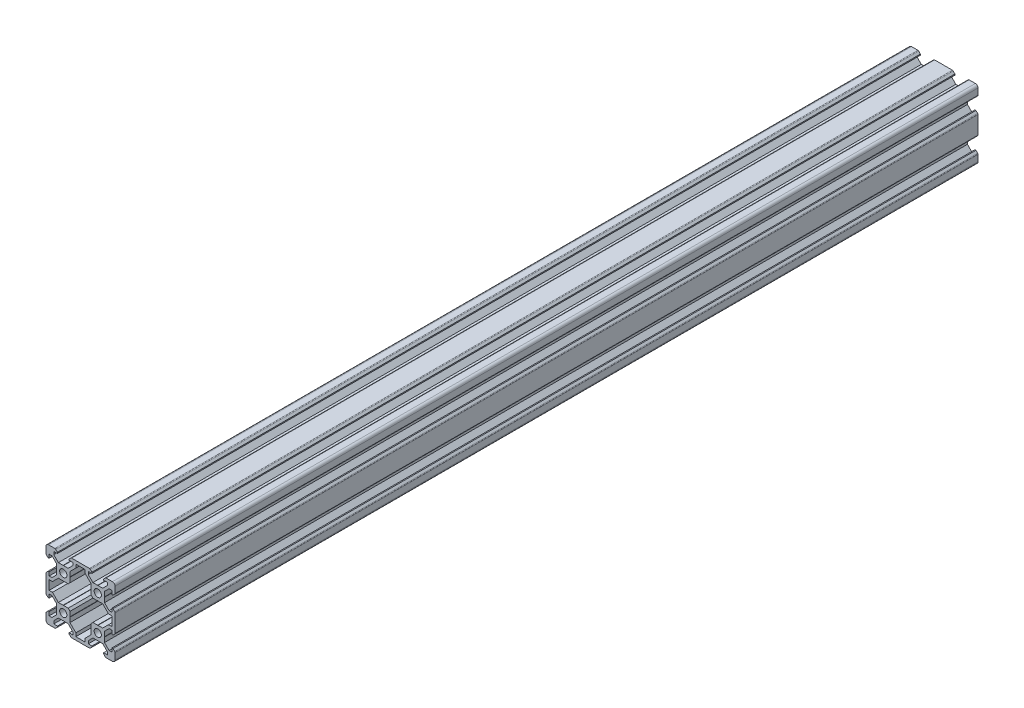
SolidWorks part; units mm, degrees
material "6063-T5"
ref_plane "Front" through (0, 0, 0) normal (0, 0, 1) x (1, 0, 0)
ref_plane "Top" through (0, 0, 0) normal (0, 1, 0) x (1, 0, 0)
ref_plane "Right" through (0, 0, 0) normal (1, 0, 0) x (0, 0, -1)
sketch "Sketch1" plane through (0, 0, 0) normal (0, 0, 1) x (1, 0, 0)
  line L0 (-8.5, 10) -> (-10, 8.5) construction
  line L1 (-8.5, 10) -> (-4.8628, 10)
  line L2 (-10, 8.5) -> (-10, 4.8628)
  line L3 (10, 24.069) -> (10, -33.8154) construction
  line L4 (4.8628, 10) -> (15.1372, 10)
  line L5 (-10, 10) -> (10, -10) construction
  line L6 (-10, -10) -> (10, 10) construction
  line L7 (4.8628, -30) -> (15.1372, -30)
  line L8 (-8.2, -5.5) -> (-8.2, -3.3865)
  line L9 (-5.5, 8.2) -> (-3.3865, 8.2)
  line L10 (-8.2, -12.7) -> (-8.2, -7.3)
  line L11 (-3.9005, 2.8395) -> (-6.561, 5.5)
  line L12 (-6.561, 5.5) -> (-8.2, 5.5)
  line L13 (-2.8395, -3.9005) -> (-0.1, -3.9005)
  line L14 (-3.9005, -2.8395) -> (-3.9005, -0.1)
  line L15 (-2.8395, 3.9005) -> (-0.1, 3.9005)
  line L16 (3.9005, -2.8395) -> (3.9005, -0.1)
  line L17 (-8.2, 3.3865) -> (-8.81, 3.3865)
  line L18 (-8.81, 3.3865) -> (-9.7976, 4.3741)
  line L19 (17.1605, -23.9005) -> (14.5, -26.561)
  line L20 (-2.8395, 3.9005) -> (-5.5, 6.561)
  line L21 (-5.5, 6.561) -> (-5.5, 8.2)
  line L22 (-3.3865, 8.2) -> (-3.3865, 8.81)
  line L23 (-3.3865, 8.81) -> (-4.3741, 9.7976)
  line L24 (0, 24.069) -> (0, -33.8154) construction
  line L25 (3.3865, 8.81) -> (4.3741, 9.7976)
  line L26 (3.3865, 8.2) -> (3.3865, 8.81)
  line L27 (5.5, 6.561) -> (5.5, 8.2)
  line L28 (2.8395, 3.9005) -> (5.5, 6.561)
  line L29 (3.3865, 8.2) -> (5.5, 8.2)
  line L30 (16.0995, -22.8395) -> (13.439, -25.5)
  line L31 (-0.1, 3.9005) -> (0, 3.8005)
  line L32 (0.1, 3.9005) -> (0, 3.8005)
  line L33 (0.1, 3.9005) -> (2.8395, 3.9005)
  line L34 (25.9287, 0) -> (-28.3459, 0) construction
  line L35 (-0.1, -3.9005) -> (0, -3.8005)
  line L36 (0.1, -3.9005) -> (0, -3.8005)
  line L37 (0.1, -3.9005) -> (2.8395, -3.9005)
  line L38 (-3.9005, 0.1) -> (-3.8005, 0)
  line L39 (-3.8005, 0) -> (-3.9005, -0.1)
  line L40 (-3.9005, 0.1) -> (-3.9005, 2.8395)
  line L41 (3.9005, 0.1) -> (3.8005, 0)
  line L42 (3.8005, 0) -> (3.9005, -0.1)
  line L43 (3.9005, 0.1) -> (3.9005, 2.8395)
  line L44 (14.5, -26.561) -> (14.5, -28.2)
  line L45 (16.6135, -28.2) -> (14.5, -28.2)
  line L46 (16.6135, -28.2) -> (16.6135, -28.81)
  line L47 (3.9005, 2.8395) -> (6.561, 5.5)
  line L48 (16.6135, -28.81) -> (15.6259, -29.7976)
  line L49 (7.3, -28.2) -> (10, -28.2)
  line L50 (-2.8395, -3.9005) -> (-5.5, -6.561)
  line L51 (-3.9005, -2.8395) -> (-6.561, -5.5)
  line L52 (10, -28.2) -> (12.7, -28.2)
  line L53 (-6.561, -5.5) -> (-8.2, -5.5)
  line L54 (-8.81, -3.3865) -> (-9.7976, -4.3741)
  line L55 (-8.2, -3.3865) -> (-8.81, -3.3865)
  line L56 (7.3, -28.2) -> (7.3, -26.239)
  line L57 (7.3, -26.239) -> (6.561, -25.5)
  line L58 (12.7, -28.2) -> (12.7, -26.239)
  line L59 (12.7, -26.239) -> (13.439, -25.5)
  line L60 (-8.2, 3.3865) -> (-8.2, 5.5)
  line L61 (-10, -4.8628) -> (-10, -15.1372)
  line L62 (-28.3459, -10) -> (-10, -10) construction
  line L63 (-3.9005, -20.1) -> (-3.9005, -22.8395)
  line L64 (-3.9005, -20.1) -> (-3.8005, -20)
  line L65 (-3.8005, -20) -> (-3.9005, -19.9)
  line L66 (3.9005, -20.1) -> (3.9005, -22.8395)
  line L67 (3.9005, -20.1) -> (3.8005, -20)
  line L68 (3.8005, -20) -> (3.9005, -19.9)
  line L69 (12.7, 8.2) -> (12.7, 6.239)
  line L70 (7.3, 8.2) -> (7.3, 6.239)
  line L71 (3.9005, -17.1605) -> (3.9005, -19.9)
  line L72 (-3.9005, -17.1605) -> (-3.9005, -19.9)
  line L73 (-3.9005, -17.1605) -> (-6.561, -14.5)
  line L74 (-6.561, -14.5) -> (-8.2, -14.5)
  line L75 (-8.2, -16.6135) -> (-8.81, -16.6135)
  line L76 (-8.81, -16.6135) -> (-9.7976, -15.6259)
  line L77 (10, 8.2) -> (12.7, 8.2)
  line L78 (7.3, 8.2) -> (10, 8.2)
  line L79 (-2.8395, -16.0995) -> (-5.5, -13.439)
  line L80 (-2.8395, -16.0995) -> (-0.1, -16.0995)
  line L81 (-0.1, -16.0995) -> (0, -16.1995)
  line L82 (0.1, -16.0995) -> (0, -16.1995)
  line L83 (0.1, -16.0995) -> (2.8395, -16.0995)
  line L84 (7.3, 6.239) -> (6.561, 5.5)
  line L85 (-8.2, -16.6135) -> (-8.2, -14.5)
  line L86 (14.5, 6.561) -> (14.5, 8.2)
  line L87 (2.8395, -23.9005) -> (5.5, -26.561)
  line L88 (-2.8395, -23.9005) -> (-5.5, -26.561)
  line L89 (-0.1, -23.9005) -> (0, -23.8005)
  line L90 (0.1, -23.9005) -> (0, -23.8005)
  line L91 (0.1, -23.9005) -> (2.8395, -23.9005)
  line L92 (-2.8395, -23.9005) -> (-0.1, -23.9005)
  line L93 (-10, -28.5) -> (-10, -24.8628)
  line L94 (16.6135, 8.2) -> (14.5, 8.2)
  line L95 (16.6135, 8.81) -> (15.6259, 9.7976)
  line L96 (-8.81, -23.3865) -> (-9.7976, -24.3741)
  line L97 (-8.2, -23.3865) -> (-8.81, -23.3865)
  line L98 (16.6135, 8.2) -> (16.6135, 8.81)
  line L99 (16.0995, 2.8395) -> (13.439, 5.5)
  line L100 (-8.2, -23.3865) -> (-8.2, -25.5)
  line L101 (-6.561, -25.5) -> (-8.2, -25.5)
  line L102 (12.7, 6.239) -> (13.439, 5.5)
  line L103 (3.9005, -22.8395) -> (6.561, -25.5)
  line L104 (-3.9005, -22.8395) -> (-6.561, -25.5)
  line L105 (-5.5, -28.2) -> (-3.3865, -28.2)
  line L106 (3.3865, -28.2) -> (5.5, -28.2)
  line L107 (3.3865, -28.2) -> (3.3865, -28.81)
  line L108 (3.3865, -28.81) -> (4.3741, -29.7976)
  line L109 (-3.3865, -28.2) -> (-3.3865, -28.81)
  line L110 (-3.3865, -28.81) -> (-4.3741, -29.7976)
  line L111 (-8.5, -30) -> (-4.8628, -30)
  line L112 (17.1605, 3.9005) -> (14.5, 6.561)
  line L113 (-5.5, -26.561) -> (-5.5, -28.2)
  line L114 (5.5, -26.561) -> (5.5, -28.2)
  line L115 (-6.239, -7.3) -> (-8.2, -7.3)
  line L116 (-5.5, -6.561) -> (-6.239, -7.3)
  line L117 (3.9005, -2.8395) -> (2.8395, -3.9005)
  line L118 (2.8395, -16.0995) -> (3.9005, -17.1605)
  line L119 (-6.239, -12.7) -> (-8.2, -12.7)
  line L120 (-5.5, -13.439) -> (-6.239, -12.7)
  line L121 (16.0995, -2.8395) -> (17.1605, -3.9005)
  line L122 (17.1605, -16.0995) -> (16.0995, -17.1605)
  line L123 (28.2, -16.6135) -> (28.81, -16.6135)
  line L124 (20.1, -3.9005) -> (20, -3.8005)
  line L125 (10, -10) -> (25.9287, -10) construction
  line L126 (19.9, -3.9005) -> (20, -3.8005)
  line L127 (19.9, -3.9005) -> (17.1605, -3.9005)
  line L128 (22.8395, -3.9005) -> (20.1, -3.9005)
  line L129 (23.9005, -2.8395) -> (23.9005, -0.1)
  line L130 (23.8005, 0) -> (23.9005, -0.1)
  line L131 (23.9005, 0.1) -> (23.8005, 0)
  line L132 (23.9005, 0.1) -> (23.9005, 2.8395)
  line L133 (20.1, 3.9005) -> (20, 3.8005)
  line L134 (19.9, 3.9005) -> (20, 3.8005)
  line L135 (16.0995, 0.1) -> (16.1995, 0)
  line L136 (16.1995, 0) -> (16.0995, -0.1)
  line L137 (22.8395, 3.9005) -> (20.1, 3.9005)
  line L138 (19.9, 3.9005) -> (17.1605, 3.9005)
  line L139 (16.0995, 0.1) -> (16.0995, 2.8395)
  line L140 (16.0995, -2.8395) -> (16.0995, -0.1)
  line L141 (20.1, -23.9005) -> (20, -23.8005)
  line L142 (19.9, -23.9005) -> (20, -23.8005)
  line L143 (19.9, -23.9005) -> (17.1605, -23.9005)
  line L144 (22.8395, -23.9005) -> (20.1, -23.9005)
  line L145 (16.0995, -17.1605) -> (16.0995, -19.9)
  line L146 (16.1995, -20) -> (16.0995, -19.9)
  line L147 (16.0995, -20.1) -> (16.1995, -20)
  line L148 (16.0995, -20.1) -> (16.0995, -22.8395)
  line L149 (19.9, -16.0995) -> (20, -16.1995)
  line L150 (20.1, -16.0995) -> (20, -16.1995)
  line L151 (19.9, -16.0995) -> (17.1605, -16.0995)
  line L152 (22.8395, -16.0995) -> (20.1, -16.0995)
  line L153 (23.9005, -17.1605) -> (23.9005, -19.9)
  line L154 (23.8005, -20) -> (23.9005, -19.9)
  line L155 (23.9005, -20.1) -> (23.8005, -20)
  line L156 (23.9005, -20.1) -> (23.9005, -22.8395)
  line L157 (25.5, -26.561) -> (25.5, -28.2)
  line L158 (26.561, -25.5) -> (28.2, -25.5)
  line L159 (28.2, -23.3865) -> (28.2, -25.5)
  line L160 (28.2, -23.3865) -> (28.81, -23.3865)
  line L161 (28.81, -23.3865) -> (29.7976, -24.3741)
  line L162 (30, -28.5) -> (30, -24.8628)
  line L163 (25.5, -28.2) -> (23.3865, -28.2)
  line L164 (23.3865, -28.2) -> (23.3865, -28.81)
  line L165 (23.3865, -28.81) -> (24.3741, -29.7976)
  line L166 (28.5, -30) -> (24.8628, -30)
  line L167 (25.5, 6.561) -> (25.5, 8.2)
  line L168 (25.5, 8.2) -> (23.3865, 8.2)
  line L169 (23.3865, 8.2) -> (23.3865, 8.81)
  line L170 (23.3865, 8.81) -> (24.3741, 9.7976)
  line L171 (28.5, 10) -> (24.8628, 10)
  line L172 (26.561, 5.5) -> (28.2, 5.5)
  line L173 (28.2, 3.3865) -> (28.2, 5.5)
  line L174 (30, 8.5) -> (30, 4.8628)
  line L175 (28.81, 3.3865) -> (29.7976, 4.3741)
  line L176 (28.2, 3.3865) -> (28.81, 3.3865)
  line L177 (23.9005, -22.8395) -> (26.561, -25.5)
  line L178 (22.8395, -23.9005) -> (25.5, -26.561)
  line L179 (22.8395, 3.9005) -> (25.5, 6.561)
  line L180 (23.9005, 2.8395) -> (26.561, 5.5)
  line L181 (28.2, -3.3865) -> (28.81, -3.3865)
  line L182 (28.81, -3.3865) -> (29.7976, -4.3741)
  line L183 (28.81, -16.6135) -> (29.7976, -15.6259)
  line L184 (30, -4.8628) -> (30, -15.1372)
  line L185 (28.2, -5.5) -> (28.2, -3.3865)
  line L186 (28.2, -16.6135) -> (28.2, -14.5)
  line L187 (23.9005, -17.1605) -> (26.561, -14.5)
  line L188 (23.9005, -2.8395) -> (26.561, -5.5)
  line L189 (26.561, -5.5) -> (28.2, -5.5)
  line L190 (26.561, -14.5) -> (28.2, -14.5)
  line L191 (26.239, -7.3) -> (28.2, -7.3)
  line L192 (26.239, -12.7) -> (28.2, -12.7)
  line L193 (28.2, -12.7) -> (28.2, -7.3)
  line L194 (22.8395, -16.0995) -> (25.5, -13.439)
  line L195 (22.8395, -3.9005) -> (25.5, -6.561)
  line L196 (25.5, -13.439) -> (26.239, -12.7)
  line L197 (25.5, -6.561) -> (26.239, -7.3)
  circle A0 centre (0, 0) radius 2.1
  arc A1 (-8.5, 10) -> (-10, 8.5) centre (-8.5, 8.5) ccw
  arc A2 (15.1372, -30) -> (15.6259, -29.7976) centre (15.1372, -29.3088) ccw
  arc A3 (-4.3741, 9.7976) -> (-4.8628, 10) centre (-4.8628, 9.3088) ccw
  arc A4 (4.8628, 10) -> (4.3741, 9.7976) centre (4.8628, 9.3088) ccw
  circle A5 centre (0, -20) radius 2.1
  arc A6 (15.1372, 10) -> (15.6259, 9.7976) centre (15.1372, 9.3088) cw
  arc A7 (-10, 4.8628) -> (-9.7976, 4.3741) centre (-9.3088, 4.8628) ccw
  arc A8 (-10, -4.8628) -> (-9.7976, -4.3741) centre (-9.3088, -4.8628) cw
  arc A9 (30, -4.8628) -> (29.7976, -4.3741) centre (29.3088, -4.8628) ccw
  arc A10 (-10, -15.1372) -> (-9.7976, -15.6259) centre (-9.3088, -15.1372) ccw
  arc A11 (30, -15.1372) -> (29.7976, -15.6259) centre (29.3088, -15.1372) cw
  arc A12 (-10, -24.8628) -> (-9.7976, -24.3741) centre (-9.3088, -24.8628) cw
  arc A14 (4.8628, -30) -> (4.3741, -29.7976) centre (4.8628, -29.3088) cw
  arc A15 (-4.3741, -29.7976) -> (-4.8628, -30) centre (-4.8628, -29.3088) cw
  arc A16 (-8.5, -30) -> (-10, -28.5) centre (-8.5, -28.5) cw
  circle A18 centre (20, 0) radius 2.1
  circle A19 centre (20, -20) radius 2.1
  arc A20 (30, -24.8628) -> (29.7976, -24.3741) centre (29.3088, -24.8628) ccw
  arc A21 (28.5, -30) -> (30, -28.5) centre (28.5, -28.5) ccw
  arc A22 (24.3741, -29.7976) -> (24.8628, -30) centre (24.8628, -29.3088) ccw
  arc A23 (24.3741, 9.7976) -> (24.8628, 10) centre (24.8628, 9.3088) cw
  arc A24 (28.5, 10) -> (30, 8.5) centre (28.5, 8.5) cw
  arc A25 (30, 4.8628) -> (29.7976, 4.3741) centre (29.3088, 4.8628) cw
  point P17 (-9.25, 9.25)
  point P68 (10, -30)
  dimension "D2" = 4.2
  dimension "D4" = 1.5
  dimension "D3" = 20
  dimension "D5" = 0.529
  dimension "D6" = 6.773
  dimension "D7" = 90
  dimension "D8" = 11
  dimension "D9" = 0.61
  dimension "D10" = 0.1
  dimension "D11" = 0.1
  dimension "D12" = 0.1
  dimension "D13" = 0.1
  dimension "D14" = 5.679
  dimension "D15" = 1.639
  dimension "D16" = 1.8
  dimension "D17" = 90
  dimension "D18" = 6.773
  dimension "D19" = 10
  dimension "D20" = 20
  dimension "D21" = 1.8
  dimension "D22" = 1.8
extrude "Boss-Extrude2" add sketch "Sketch1" along normal blind 500
